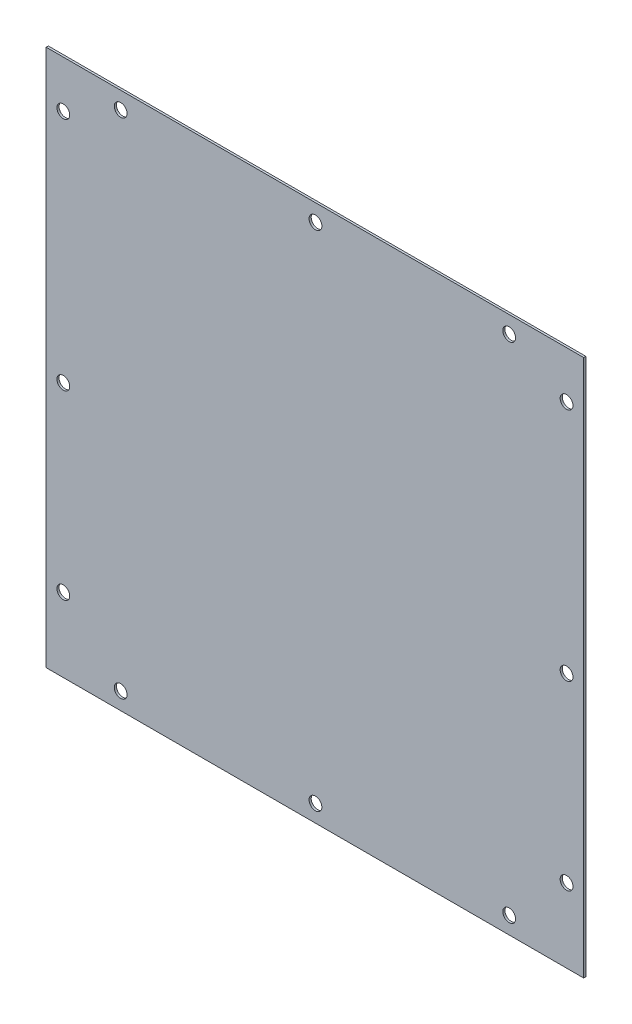
SolidWorks part; units mm, degrees
ref_plane "Alzado" through (0, 0, 0) normal (0, 0, 1) x (1, 0, 0)
ref_plane "Planta" through (0, 0, 0) normal (0, 1, 0) x (1, 0, 0)
ref_plane "Vista lateral" through (0, 0, 0) normal (1, 0, 0) x (0, 0, -1)
sketch "Croquis1" plane through (0, 0, 0) normal (0, 0, 1) x (1, 0, 0)
  line L0 (25.4, 0) -> (25.4, 400) construction
  line L1 (0, 0) -> (400, 0)
  line L2 (0, 0) -> (0, 400)
  line L3 (0, 400) -> (400, 400)
  line L4 (400, 0) -> (400, 400)
  line L5 (374.6, 400) -> (374.6, 0) construction
  line L6 (25.4, 374.6) -> (374.6, 374.6) construction
  line L7 (25.4, 25.4) -> (374.6, 25.4) construction
  line L8 (20.9941, 387.3) -> (12.7, 387.3) construction
  line L9 (12.7, 387.3) -> (12.7, 376.2436) construction
  line L10 (380.3451, 12.7) -> (387.3, 12.7) construction
  line L11 (387.3, 12.7) -> (387.3, 24.8661) construction
  circle A0 centre (55.4, 387.3) radius 4.7625
  circle A1 centre (200.4, 387.3) radius 4.7625
  circle A2 centre (344.6, 387.3) radius 4.7625
  circle A3 centre (12.7, 365) radius 4.7625
  circle A4 centre (12.7, 190) radius 4.7625
  circle A5 centre (12.7, 55) radius 4.7625
  circle A6 centre (387.3, 365) radius 4.7625
  circle A7 centre (387.3, 190) radius 4.7625
  circle A8 centre (387.3, 55) radius 4.7625
  circle A9 centre (344.6, 12.7) radius 4.7625
  circle A10 centre (200.4, 12.7) radius 4.7625
  circle A11 centre (55.4, 12.7) radius 4.7625
  point P43 (387.3, 18.7831)
  point P44 (0, 0)
  point P45 (0, 0)
  point P46 (0, 0)
  point P47 (0, 0)
  point P48 (390.7511, 372.3076)
  point P49 (0, 0)
  point P50 (0, 0)
  point P51 (381.7181, 365)
  point P52 (0, 0)
  point P53 (0, 0)
  point P54 (0, 0)
  point P55 (0, 0)
  point P56 (0, 0)
  point P57 (0, 0)
  dimension "D17" = 9.525
  dimension "D1" = 400
  dimension "D2" = 400
  dimension "D3" = 25.4
  dimension "D4" = 25.4
  dimension "D5" = 25.4
  dimension "D6" = 25.4
  dimension "D7" = 30
  dimension "D8" = 30
  dimension "D9" = 145
  dimension "D10" = 310
  dimension "D11" = 35
  dimension "D12" = 175
  dimension "D13" = 12.7
  dimension "D14" = 12.7
  dimension "D15" = 12.7
  dimension "D16" = 12.7
extrude "Saliente-Extruir1" add sketch "Croquis1" along normal blind 1.5875
